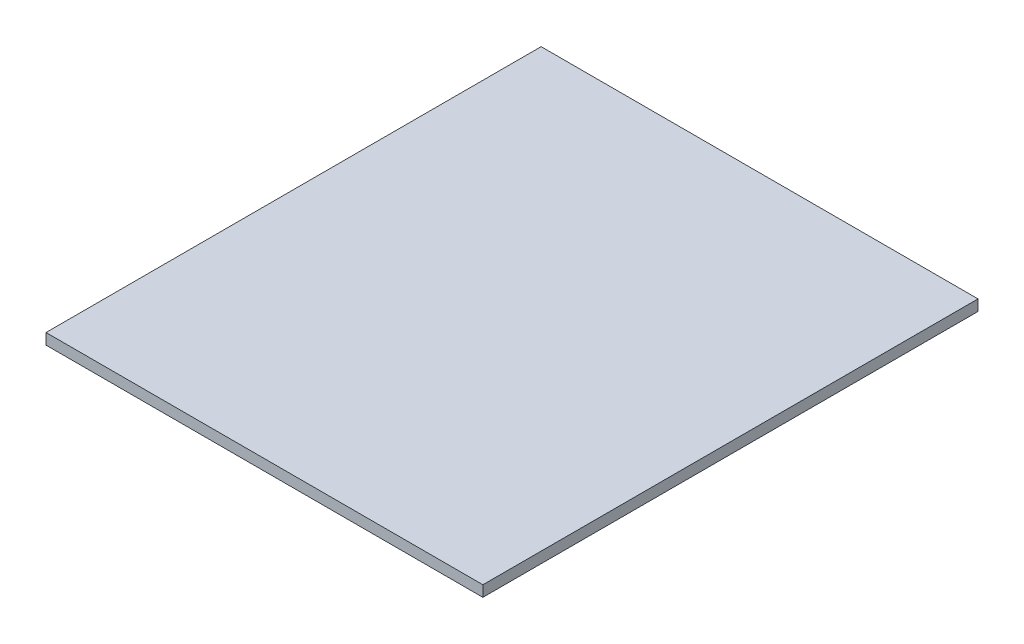
SolidWorks part; units mm, degrees
ref_plane "Front Plane" through (0, 0, 0) normal (0, 0, 1) x (1, 0, 0)
ref_plane "Top Plane" through (0, 0, 0) normal (0, 1, 0) x (1, 0, 0)
ref_plane "Right Plane" through (0, 0, 0) normal (1, 0, 0) x (0, 0, -1)
sketch "Sketch1" plane through (0, 0, 0) normal (0, 1, 0) x (1, 0, 0)
  line L1 (0, 0) -> (120, 0)
  line L2 (0, 0) -> (0, 136)
  line L3 (0, 136) -> (120, 136)
  line L4 (120, 0) -> (120, 136)
  dimension "D1" = 136
  dimension "D2" = 120
extrude "Boss-Extrude1" add sketch "Sketch1" along normal blind 3
